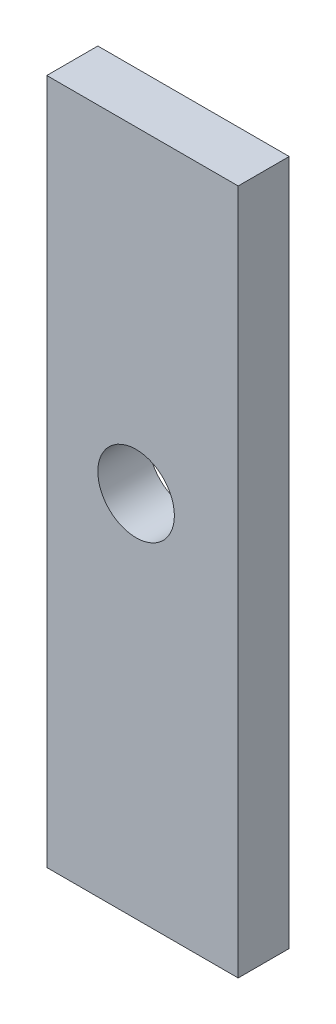
SolidWorks part; units mm, degrees
ref_plane "Front Plane" through (0, 0, 0) normal (0, 0, 1) x (1, 0, 0)
ref_plane "Top Plane" through (0, 0, 0) normal (0, 1, 0) x (1, 0, 0)
ref_plane "Right Plane" through (0, 0, 0) normal (1, 0, 0) x (0, 0, -1)
sketch "Sketch1" plane through (0, 0, 0) normal (0, 0, 1) x (1, 0, 0)
  line L0 (-3.5, 12.44) -> (4, 12.44)
  line L1 (-3.5, -14.441) -> (4, -14.441)
  line L2 (4, -14.441) -> (4, 12.44)
  line L3 (-3.5, 12.44) -> (-3.5, -14.441)
  circle A0 centre (0, 0) radius 1.5
  dimension "D1" = 3
  dimension "D4" = 12.44
  dimension "D2" = 4
  dimension "D3" = 3.5
  dimension "D5" = 14.441
extrude "Boss-Extrude1" add sketch "Sketch1" along normal blind 2
equation "\"D5@Sketch1\" = \"D76@Sketch1@palmUp.SLDPRT\" - 6.72 - 0.41'Support Pully Thumb Palm Up"
